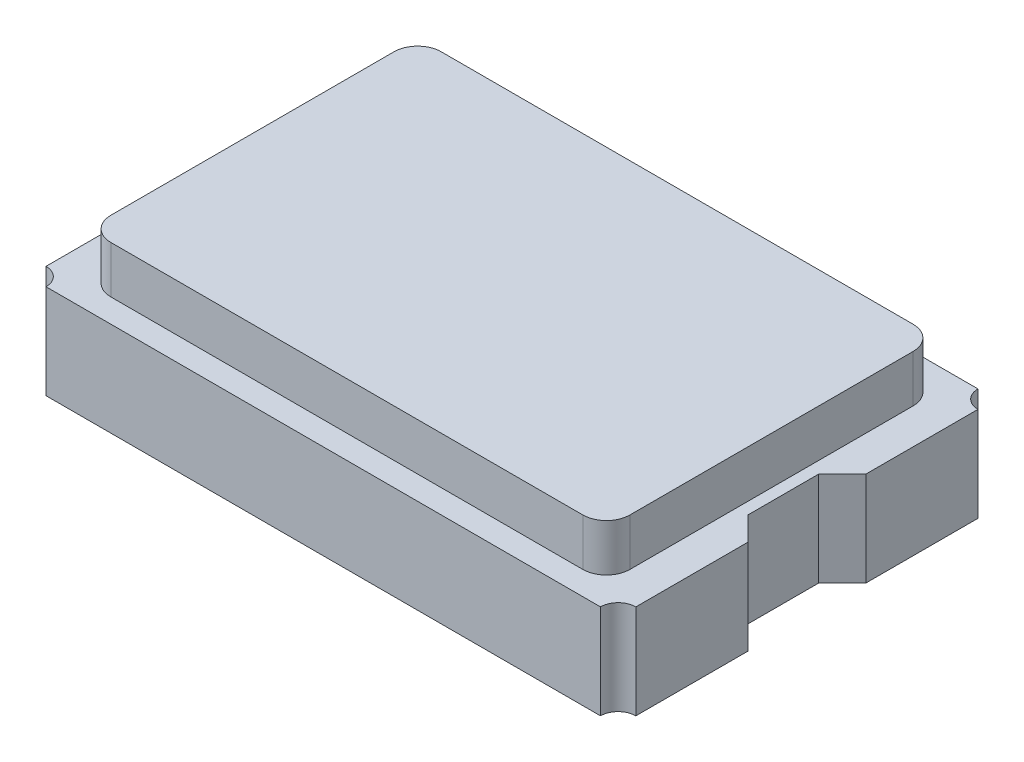
SolidWorks part; units mm, degrees
ref_plane "Front Plane" through (0, 0, 0) normal (0, 0, 1) x (1, 0, 0)
ref_plane "Top Plane" through (0, 0, 0) normal (0, 1, 0) x (1, 0, 0)
ref_plane "Right Plane" through (0, 0, 0) normal (1, 0, 0) x (0, 0, -1)
sketch "Sketch1" plane through (0, 0, 0) normal (0, 1, 0) x (1, 0, 0)
  line L1 (-2.5, -1.6) -> (2.5, -1.6)
  line L2 (-2.5, -1.6) -> (-2.5, 1.6)
  line L3 (-2.5, 1.6) -> (2.5, 1.6)
  line L4 (2.5, -1.6) -> (2.5, 1.6)
  line L5 (-2.5, -1.6) -> (2.5, 1.6) construction
  line L6 (-2.5, 1.6) -> (2.5, -1.6) construction
  point P0 (0, 0)
  dimension "D1" = 5
  dimension "D2" = 3.2
extrude "Boss-Extrude1" add sketch "Sketch1" along normal blind 0.8
sketch "Sketch2" plane through (0, 0.8, 0) normal (0, 1, 0) x (1, 0, 0)
  line L0 (0, 1.6) -> (0, -1.6) construction
  line L1 (2.5, 1.6) -> (-2.5, 1.6) construction
  line L2 (-2.5, -1.6) -> (2.5, -1.6) construction
  line L3 (-2.5, 0) -> (2.5, 0) construction
  line L4 (-2.5, 1.6) -> (-2.5, -1.6) construction
  line L5 (2.5, -1.6) -> (2.5, 1.6) construction
  line L6 (-2.3, -0.3) -> (-2.3, 0.3)
  line L7 (-2.3, 0.3) -> (-2.5, 0.5)
  line L8 (-2.5, 0.5) -> (-2.5, -0.5)
  line L9 (-2.3, -0.3) -> (-2.5, -0.5)
  line L10 (2.3, -0.3) -> (2.5, -0.5)
  line L11 (2.5, 0.5) -> (2.5, -0.5)
  line L12 (2.3, 0.3) -> (2.5, 0.5)
  line L13 (2.3, -0.3) -> (2.3, 0.3)
  circle A0 centre (-2.5, 1.6) radius 0.15
  circle A1 centre (2.5, 1.6) radius 0.15
  circle A2 centre (2.5, -1.6) radius 0.15
  circle A3 centre (-2.5, -1.6) radius 0.15
  point P26 (-2.3, 0)
  point P30 (2.3, 0)
  dimension "D1" = 0.3
  dimension "D2" = 0.2
  dimension "D3" = 0.3
  dimension "D4" = 135
extrude "Cut-Extrude1" cut sketch "Sketch2" against normal up to next
sketch "Sketch3" plane through (0, 0.8, 0) normal (0, 1, 0) x (1, 0, 0)
  line L0 (2.5, 0.5) -> (2.5, 1.45) construction
  line L1 (-2, -1.4) -> (2, -1.4)
  line L2 (-2.2, -1.2) -> (-2.2, 1.2)
  line L3 (-2, 1.4) -> (2, 1.4)
  line L4 (2.2, -1.2) -> (2.2, 1.2)
  line L5 (-2.2, -1.4) -> (2.2, 1.4) construction
  line L6 (-2.2, 1.4) -> (2.2, -1.4) construction
  line L7 (2.35, 1.6) -> (-2.35, 1.6) construction
  arc A0 (2, 1.4) -> (2.2, 1.2) centre (2, 1.2) cw
  arc A1 (2, -1.4) -> (2.2, -1.2) centre (2, -1.2) ccw
  arc A2 (-2, -1.4) -> (-2.2, -1.2) centre (-2, -1.2) cw
  arc A3 (-2.2, 1.2) -> (-2, 1.4) centre (-2, 1.2) cw
  point P0 (0, 0)
  dimension "D3" = 0.2
  dimension "D1" = 0.3
  dimension "D2" = 0.2
extrude "Boss-Extrude3" add sketch "Sketch3" along normal blind 0.4
